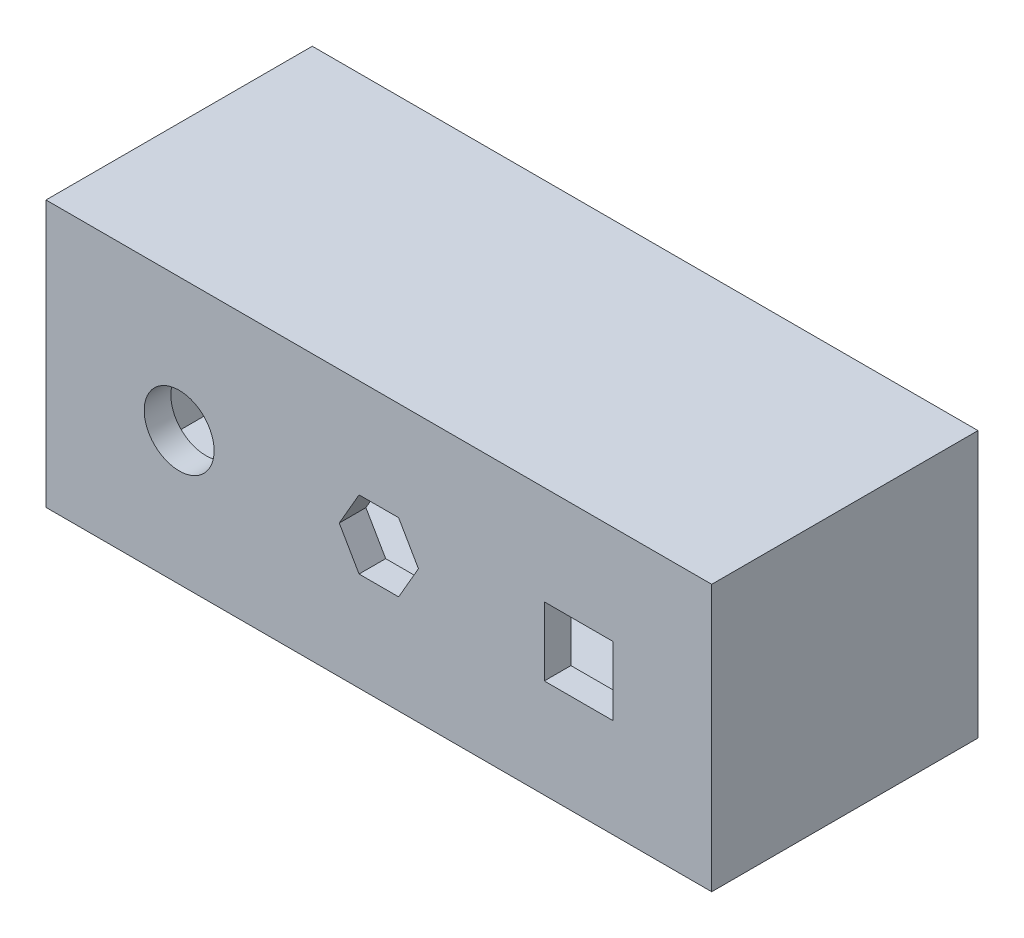
SolidWorks part; units mm, degrees
material "Beech"
ref_plane "Front Plane" through (0, 0, 0) normal (0, 0, 1) x (1, 0, 0)
ref_plane "Top Plane" through (0, 0, 0) normal (0, 1, 0) x (1, 0, 0)
ref_plane "Right Plane" through (0, 0, 0) normal (1, 0, 0) x (0, 0, -1)
sketch "Sketch5" plane through (0, 0, 0) normal (0, 0, 1) x (1, 0, 0)
  line L1 (-250, -100) -> (250, -100)
  line L2 (-250, -100) -> (-250, 100)
  line L3 (-250, 100) -> (250, 100)
  line L4 (250, -100) -> (250, 100)
  line L5 (-250, -100) -> (250, 100) construction
  line L6 (-250, 100) -> (250, -100) construction
  point P0 (0, 0)
  dimension "D1" = 200
  dimension "D2" = 500
extrude "Boss-Extrude2" add sketch "Sketch5" along normal blind 200
shell "Shell2" thickness 20
sketch "Sketch6" plane through (0, 0, 200) normal (0, 0, 1) x (1, 0, 0)
  line L0 (-250, 0) -> (250, 0) construction
  line L1 (14.8668, 25.75) -> (-14.8668, 25.75)
  line L2 (-14.8668, 25.75) -> (-29.7335, 0)
  line L3 (-29.7335, 0) -> (-14.8668, -25.75)
  line L4 (-14.8668, -25.75) -> (14.8668, -25.75)
  line L5 (14.8668, -25.75) -> (29.7335, 0)
  line L6 (29.7335, 0) -> (14.8668, 25.75)
  line L7 (124.25, -25.75) -> (175.75, -25.75)
  line L8 (124.25, -25.75) -> (124.25, 25.75)
  line L9 (124.25, 25.75) -> (175.75, 25.75)
  line L10 (175.75, -25.75) -> (175.75, 25.75)
  line L11 (124.25, -25.75) -> (175.75, 25.75) construction
  line L12 (124.25, 25.75) -> (175.75, -25.75) construction
  line L13 (-250, 100) -> (-250, -100) construction
  line L14 (0, -100) -> (0, 0) construction
  line L15 (-250, -100) -> (250, -100) construction
  line L16 (250, -100) -> (250, 100) construction
  circle A0 centre (0, 0) radius 25.75 construction
  circle A1 centre (-150, 0) radius 26.25
  point P11 (150, 0)
  dimension "D3" = 52.5
  dimension "D4" = 51.5
  dimension "D1" = 150
  dimension "D2" = 150
  dimension "D5" = 51.5
extrude "Cut-Extrude2" cut sketch "Sketch6" against normal blind 51.6
